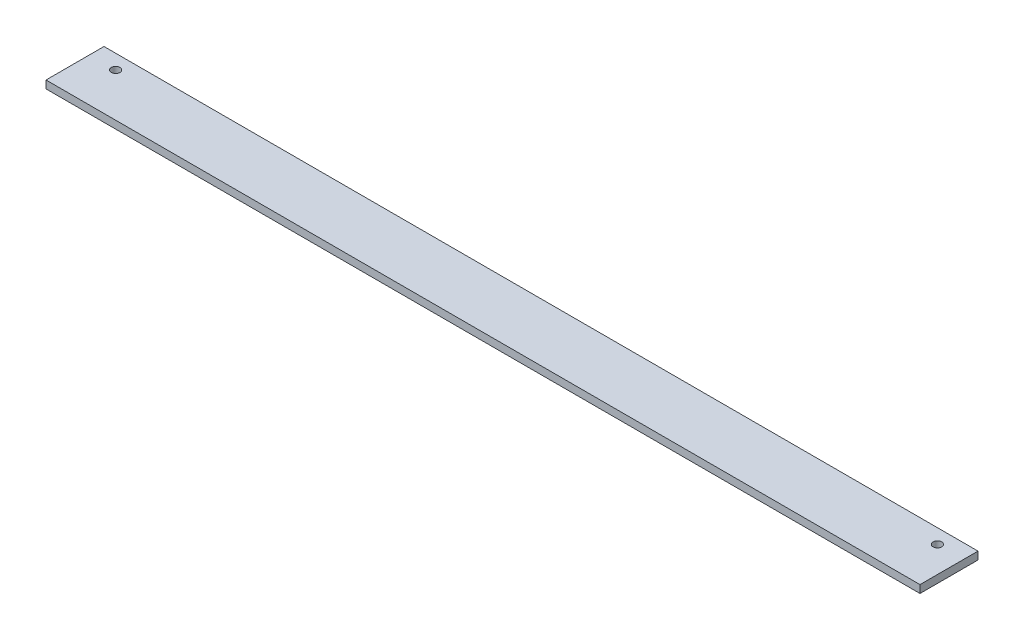
SolidWorks part; units mm, degrees
ref_plane "Спереди" through (0, 0, 0) normal (0, 0, 1) x (1, 0, 0)
ref_plane "Сверху" through (0, 0, 0) normal (0, 1, 0) x (1, 0, 0)
ref_plane "Справа" through (0, 0, 0) normal (1, 0, 0) x (0, 0, -1)
sketch "Эскиз1" plane through (0, 0, 0) normal (1, 0, 0) x (0, 0, -1)
  line L1 (-15, -2) -> (15, -2)
  line L2 (-15, -2) -> (-15, 2)
  line L3 (-15, 2) -> (15, 2)
  line L4 (15, -2) -> (15, 2)
  line L5 (-15, -2) -> (15, 2) construction
  line L6 (-15, 2) -> (15, -2) construction
  point P0 (0, 0)
  dimension "D1" = 4
  dimension "D2" = 30
extrude "Бобышка-Вытянуть1" add sketch "Эскиз1" along normal blind 452
sketch "Эскиз2" plane through (0, 2, 0) normal (0, 1, 0) x (1, 0, 0)
  line L0 (452, 15) -> (0, 15) construction
  line L1 (0, 15) -> (0, -15) construction
  line L2 (452, 15) -> (452, -15) construction
  circle A0 centre (13.5, 7.5) radius 2.25
  circle A1 centre (438.5, 7.5) radius 2.25
  dimension "D1" = 4.5
  dimension "D4" = 4.5
  dimension "D2" = 7.5
  dimension "D3" = 13.5
  dimension "D5" = 13.5
  dimension "D6" = 7.5
extrude "Вырез-Вытянуть1" cut sketch "Эскиз2" against normal through all
